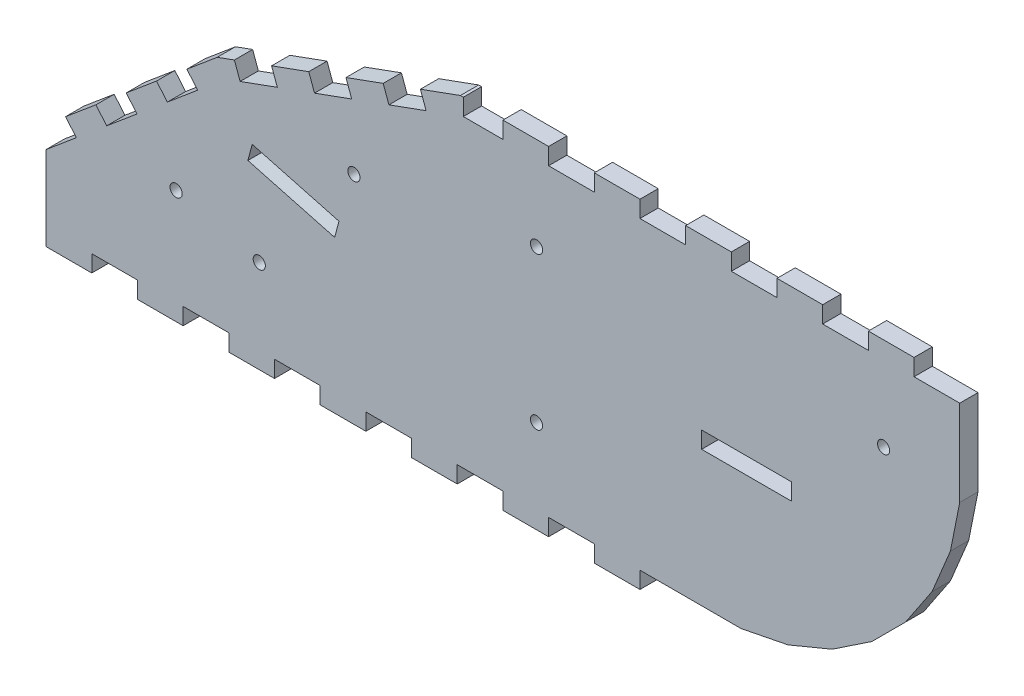
SolidWorks part; units mm, degrees
ref_plane "Front Plane" through (0, 0, 0) normal (0, 0, 1) x (1, 0, 0)
ref_plane "Top Plane" through (0, 0, 0) normal (0, 1, 0) x (1, 0, 0)
ref_plane "Right Plane" through (0, 0, 0) normal (1, 0, 0) x (0, 0, -1)
sketch "Model" plane through (0, 0, 0) normal (0, 0, 1) x (1, 0, 0)
  line L0 (41.3057, 60.3175) -> (37.7654, 64.5367)
  line L1 (296.4555, 118.6634) -> (281.4555, 118.6634)
  line L2 (266.4555, 118.6634) -> (251.4555, 118.6634)
  line L3 (236.4555, 118.6634) -> (221.4555, 118.6634)
  line L4 (206.4555, 118.6634) -> (191.4555, 118.6634)
  line L5 (176.4555, 118.6634) -> (161.4555, 118.6634)
  line L6 (236.4555, 13.1634) -> (239.6821, 13.1634)
  line L7 (239.6821, 13.1634) -> (255.0635, 16.2229)
  line L8 (255.0635, 16.2229) -> (269.5524, 22.2245)
  line L9 (269.5524, 22.2245) -> (282.5922, 30.9373)
  line L10 (282.5922, 30.9373) -> (293.6815, 42.0267)
  line L11 (293.6815, 42.0267) -> (302.3944, 55.0664)
  line L12 (302.3944, 55.0664) -> (308.3959, 69.5554)
  line L13 (308.3959, 69.5554) -> (311.4555, 84.9368)
  line L14 (311.4555, 84.9368) -> (311.4555, 100.6195)
  line L15 (296.4555, 118.6634) -> (296.4555, 113.1634)
  line L16 (281.4555, 118.6634) -> (281.4555, 113.1634)
  line L17 (281.4555, 113.1634) -> (266.4555, 113.1634)
  line L18 (266.4555, 113.1634) -> (266.4555, 118.6634)
  line L19 (296.4555, 113.1634) -> (311.4555, 113.1634)
  line L20 (251.4555, 118.6634) -> (251.4555, 113.1634)
  line L21 (251.4555, 113.1634) -> (236.4555, 113.1634)
  line L22 (236.4555, 113.1634) -> (236.4555, 118.6634)
  line L23 (221.4555, 118.6634) -> (221.4555, 113.1634)
  line L24 (221.4555, 113.1634) -> (206.4555, 113.1634)
  line L25 (206.4555, 113.1634) -> (206.4555, 118.6634)
  line L26 (191.4555, 118.6634) -> (191.4555, 113.1634)
  line L27 (191.4555, 113.1634) -> (176.4555, 113.1634)
  line L28 (176.4555, 113.1634) -> (176.4555, 118.6634)
  line L29 (161.4555, 118.6634) -> (161.4555, 113.1634)
  line L30 (161.4555, 113.1634) -> (148.4555, 113.1634)
  line L31 (311.4555, 113.1634) -> (311.4555, 100.6195)
  line L32 (221.4555, 13.1634) -> (206.4555, 13.1634)
  line L33 (191.4555, 13.1634) -> (176.4555, 13.1634)
  line L34 (161.4555, 13.1634) -> (146.4555, 13.1634)
  line L35 (131.4555, 13.1634) -> (116.4555, 13.1634)
  line L36 (101.4555, 13.1634) -> (86.4555, 13.1634)
  line L37 (71.4555, 13.1634) -> (56.4555, 13.1634)
  line L38 (41.4555, 13.1634) -> (26.4555, 13.1634)
  line L39 (11.4254, 7.6634) -> (26.4555, 7.6634)
  line L40 (26.4555, 7.6634) -> (26.4555, 13.1634)
  line L41 (41.4555, 7.6634) -> (56.4555, 7.6634)
  line L42 (71.4555, 7.6634) -> (86.4555, 7.6634)
  line L43 (101.4555, 7.6634) -> (116.4555, 7.6634)
  line L44 (131.4555, 7.6634) -> (146.4555, 7.6634)
  line L45 (161.4555, 7.6634) -> (176.4555, 7.6634)
  line L46 (191.4555, 7.6634) -> (206.4555, 7.6634)
  line L47 (41.4555, 13.1634) -> (41.4555, 7.6634)
  line L48 (56.4555, 13.1634) -> (56.4555, 7.6634)
  line L49 (116.4555, 13.1634) -> (116.4555, 7.6634)
  line L50 (86.4555, 13.1634) -> (86.4555, 7.6634)
  line L51 (101.4555, 13.1634) -> (101.4555, 7.6634)
  line L52 (131.4555, 13.1634) -> (131.4555, 7.6634)
  line L53 (71.4555, 13.1634) -> (71.4555, 7.6634)
  line L54 (146.4555, 13.1634) -> (146.4555, 7.6634)
  line L55 (161.4555, 13.1634) -> (161.4555, 7.6634)
  line L56 (176.4555, 13.1634) -> (176.4555, 7.6634)
  line L57 (191.4555, 13.1634) -> (191.4555, 7.6634)
  line L58 (206.4555, 13.1634) -> (206.4555, 7.6634)
  line L59 (221.4555, 13.1634) -> (236.4555, 13.1634)
  line L60 (256.2055, 63.1634) -> (226.7055, 63.1634)
  line L61 (226.7055, 63.1634) -> (226.7055, 57.6634)
  line L62 (226.7055, 57.6634) -> (256.2055, 57.6634)
  line L63 (256.2055, 57.6634) -> (256.2055, 63.1634)
  line L64 (107.629, 62.976) -> (79.1342, 70.6111)
  line L65 (79.1342, 70.6111) -> (77.7107, 65.2986)
  line L66 (77.7107, 65.2986) -> (106.2055, 57.6634)
  line L67 (106.2055, 57.6634) -> (107.629, 62.976)
  line L68 (134.3597, 113.8867) -> (136.2408, 108.7184)
  line L69 (134.3597, 113.8867) -> (147.4876, 118.6634)
  line L70 (124.0257, 104.2739) -> (136.2408, 108.7184)
  line L71 (122.1437, 109.4405) -> (124.0257, 104.2739)
  line L72 (109.9286, 104.9959) -> (111.8097, 99.8276)
  line L73 (109.9286, 104.9959) -> (122.1437, 109.4405)
  line L74 (99.5945, 95.383) -> (111.8097, 99.8276)
  line L75 (97.7126, 100.5497) -> (99.5945, 95.383)
  line L76 (85.4974, 96.1051) -> (87.3785, 90.9368)
  line L77 (85.4974, 96.1051) -> (97.7126, 100.5497)
  line L78 (75.1633, 86.4922) -> (87.3785, 90.9368)
  line L79 (75.1633, 86.4922) -> (73.2845, 91.6558)
  line L80 (57.6832, 81.2463) -> (61.2177, 77.034)
  line L81 (47.7238, 72.891) -> (51.2622, 68.6762)
  line L82 (27.8068, 56.1804) -> (31.3424, 51.969)
  line L83 (17.8484, 47.8261) -> (21.3838, 43.6128)
  line L84 (61.2177, 77.034) -> (51.2622, 68.6762)
  line L85 (41.3057, 60.3175) -> (31.3424, 51.969)
  line L86 (21.3838, 43.6128) -> (11.4254, 35.2584)
  line L87 (73.2845, 91.6558) -> (67.6407, 89.6016)
  line L88 (67.6407, 89.6016) -> (57.6832, 81.2463)
  line L89 (47.7238, 72.891) -> (37.7654, 64.5367)
  line L90 (27.8068, 56.1804) -> (17.8484, 47.8261)
  line L91 (11.4254, 35.2584) -> (11.4254, 7.6634)
  line L92 (148.4555, 118.6634) -> (147.4876, 118.6634)
  line L93 (148.4555, 113.1634) -> (148.4555, 118.6634)
  circle A0 centre (172.4876, 88.1634) radius 2
  circle A1 centre (286.4555, 88.1634) radius 2
  circle A2 centre (81.4555, 38.1634) radius 2
  circle A3 centre (172.4876, 38.1634) radius 2
  circle A4 centre (112.543, 78.8124) radius 2
  circle A5 centre (54.155, 45.0021) radius 2
extrude "Boss-Extrude1" add sketch "Model" along normal blind 6 contours L66 L67 L64 L65 | L91 L39 L40 L38 L47 L41 L48 L37 L53 L42 L50 L36 L51 L43 L49 L35 L52 L44 L54 L34 L55 L45 L56 L33 L57 L46 L58 L32 L59 L6 L7 L8 L9 L10 L11 L12 L13 L14 L31 L19 L15 L1 L16 L17 L18 L2 L20 L21 L22 L3 L23 L24 L25 L4 L26 L27 L28 L5 L29 L30 L93 L92 L69 L68 L70 L71 L73 L72 L74 L75 L77 L76 L78 L79 L87 L88 L80 L84 L81 L89 L0 L85 L82 L90 L83 L86 | A5 | A2 | A4 | A0 | A3 | L60 L61 L62 L63 | A1
